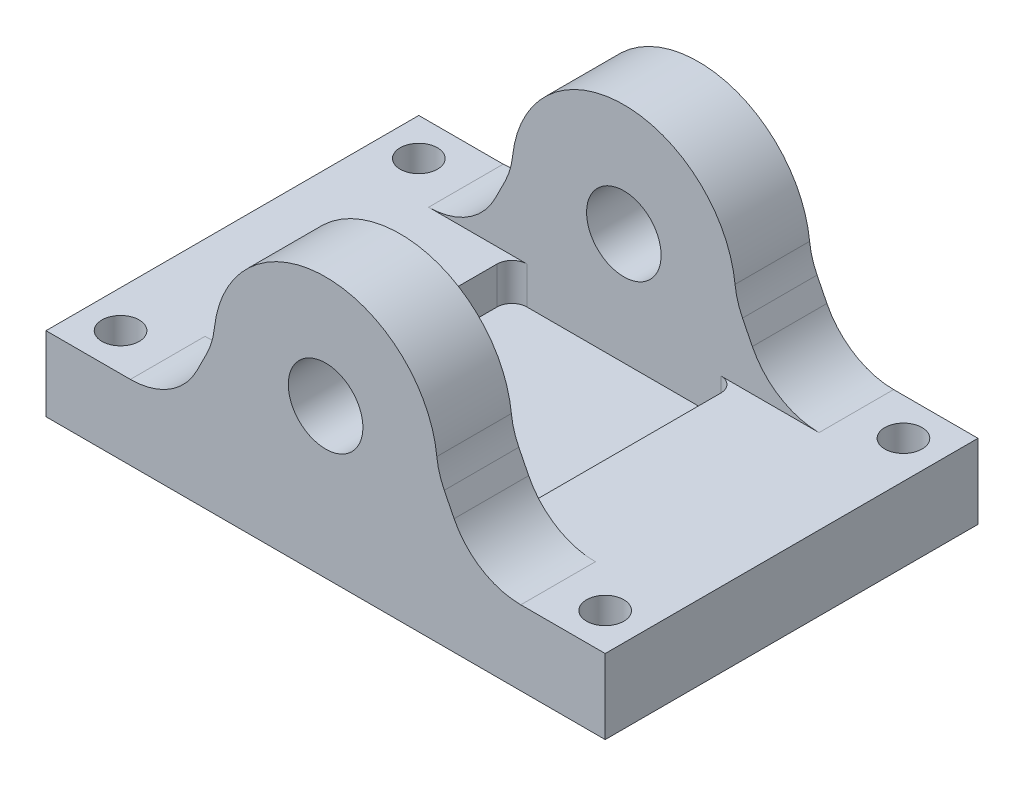
SolidWorks part; units mm, degrees
ref_plane "Front Plane" through (0, 0, 0) normal (0, 0, 1) x (1, 0, 0)
ref_plane "Top Plane" through (0, 0, 0) normal (0, 1, 0) x (1, 0, 0)
ref_plane "Right Plane" through (0, 0, 0) normal (1, 0, 0) x (0, 0, -1)
sketch "Sketch1" plane through (0, 0, 0) normal (0, 1, 0) x (1, 0, 0)
  line L1 (0, 0) -> (75, 0)
  line L2 (0, 0) -> (0, 50)
  line L3 (0, 50) -> (75, 50)
  line L4 (75, 0) -> (75, 50)
  dimension "D1" = 75
  dimension "D2" = 50
extrude "Boss-Extrude1" add sketch "Sketch1" along normal blind 10 contours L4 L3 L2 L1
sketch "Sketch2" plane through (0, 0, 0) normal (0, 0, 1) x (1, 0, 0)
  line L0 (0, 10) -> (75, 10) construction
  line L1 (75, 10) -> (75, 0) construction
  line L2 (52.5, 20) -> (57.5, 10)
  line L3 (22.5, 20) -> (17.5, 10)
  line L4 (17.5, 10) -> (57.5, 10)
  arc A0 (52.5, 20) -> (22.5, 20) centre (37.5, 20) ccw
  dimension "D1" = 30
  dimension "D2" = 10
  dimension "D3" = 37.5
  dimension "D4" = 5
  dimension "D5" = 5
extrude "Boss-Extrude2" add sketch "Sketch2" against normal blind 10
fillet "Fillet1" radius 10 4 edges at (17.5, 10, -5) (57.5, 10, -5) (22.5, 20, -5) (52.5, 20, -5)
sketch "Sketch4" plane through (0, 0, -10) normal (0, 0, -1) x (-1, 0, 0)
  line L0 (-11.3197, 10) -> (-63.6803, 10) construction
  circle A0 centre (-37.5, 20) radius 5
  dimension "D1" = 10
  dimension "D2" = 10
  dimension "D3" = 37.5
extrude "Cut-Extrude1" cut sketch "Sketch4" against normal through all
ref_plane "Plane1" through (0, 0, -25) normal (0, 0, -1) x (-1, 0, 0)
mirror "Mirror1" about plane through (0, 0, -25) normal (0, 0, -1) of "Boss-Extrude2", "Fillet1", "Cut-Extrude1"
sketch "Sketch5" plane through (0, 10, 0) normal (0, 1, 0) x (1, 0, 0)
  line L0 (0, 0) -> (0, 50) construction
  line L1 (0, 0) -> (11.3197, 0) construction
  circle A0 centre (5, 5) radius 2.5
  dimension "D1" = 5
  dimension "D2" = 5
  dimension "D3" = 5
extrude "Cut-Extrude2" cut sketch "Sketch5" against normal through all contours A0
ref_plane "Plane2" through (37.5, 0, 0) normal (1, 0, 0) x (0, 0, -1)
mirror "Mirror2" about plane through (0, 0, -25) normal (0, 0, -1) of "Cut-Extrude2"
mirror "Mirror3" about plane through (37.5, 0, 0) normal (1, 0, 0) of "Mirror2", "Cut-Extrude2"
sketch "Sketch6" plane through (0, 10, 0) normal (0, 1, 0) x (1, 0, 0)
  line L0 (11.3197, 40) -> (63.6803, 40) construction
  line L1 (63.6803, 10) -> (54.7361, 10) construction
  line L2 (22.5, 40) -> (52.5, 40)
  line L3 (22.5, 40) -> (22.5, 10)
  line L4 (22.5, 10) -> (52.5, 10)
  line L5 (52.5, 40) -> (52.5, 10)
  line L6 (37.5, -5.5) -> (37.5, 5.5) construction
  dimension "D1" = 30
  dimension "D2" = 15
extrude "Cut-Extrude3" cut sketch "Sketch6" against normal blind 5
fillet "Fillet2" radius 2 4 edges at (52.5, 7.5, -40) (22.5, 7.5, -40) (22.5, 7.5, -10) (52.5, 7.5, -10)
